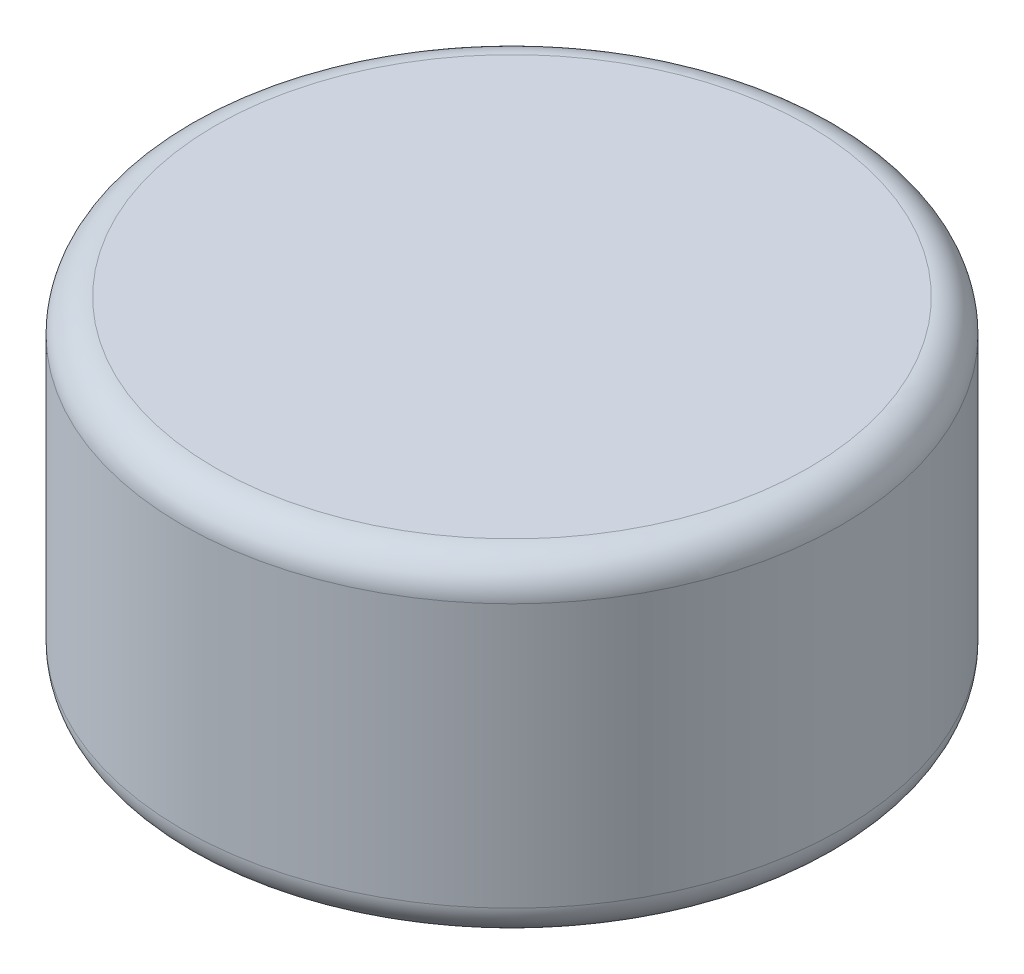
SolidWorks part; units mm, degrees
ref_plane "前视基准面" through (0, 0, 0) normal (0, 0, 1) x (1, 0, 0)
ref_plane "上视基准面" through (0, 0, 0) normal (0, 1, 0) x (1, 0, 0)
ref_plane "右视基准面" through (0, 0, 0) normal (1, 0, 0) x (0, 0, -1)
other "Configuration Table"
sketch "草图2" plane through (0, 0, 0) normal (0, 1, 0) x (1, 0, 0)
  circle A0 centre (0, 0) radius 2
  dimension "D1" = 4
extrude "凸台-拉伸1" add sketch "草图2" along normal mid plane 2
fillet "圆角1" radius 0.2 2 edges at (0, -1, 2) (0, 1, 2)
